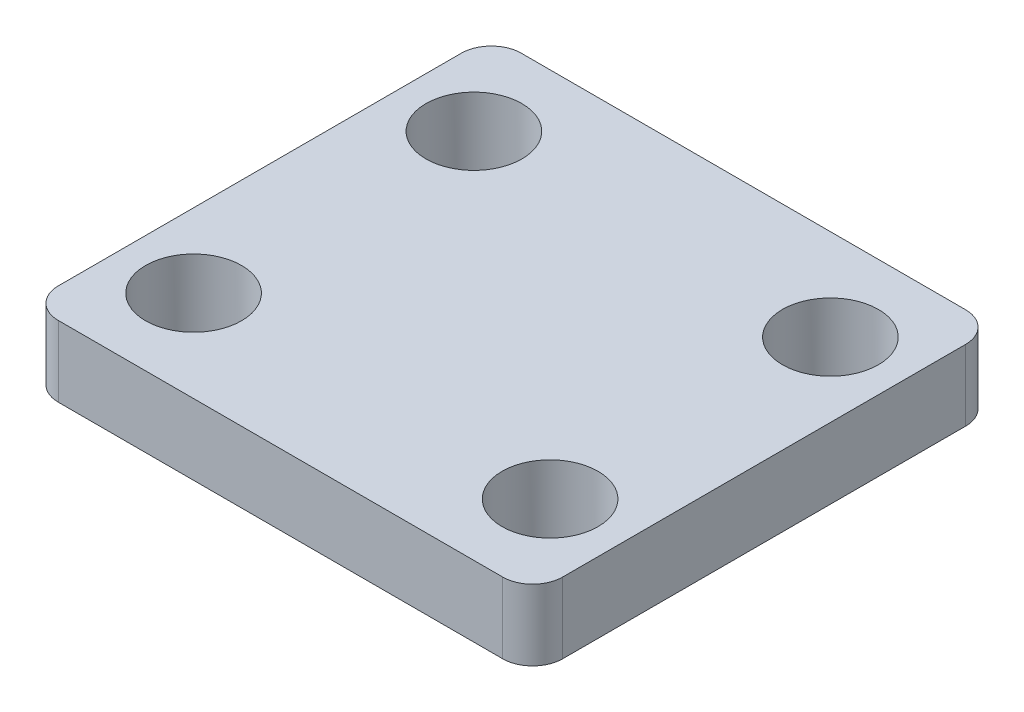
SolidWorks part; units mm, degrees
ref_plane "Plan de face" through (0, 0, 0) normal (0, 0, 1) x (1, 0, 0)
ref_plane "Plan de dessus" through (0, 0, 0) normal (0, 1, 0) x (1, 0, 0)
ref_plane "Plan de droite" through (0, 0, 0) normal (1, 0, 0) x (0, 0, -1)
ref_plane "Plan1" through (0, 12.573, 0) normal (0, 1, 0) x (1, 0, 0)
sketch "Esquisse1" plane through (0, 12.573, 0) normal (0, 1, 0) x (1, 0, 0)
  line L0 (-21.3614, 19.6088) -> (-21.3614, -19.6088)
  line L1 (-21.3614, -19.6088) -> (21.3614, -19.6088)
  line L2 (21.3614, -19.6088) -> (21.3614, 19.6088)
  line L3 (21.3614, 19.6088) -> (-21.3614, 19.6088)
extrude "Boss.-Extru.1" add sketch "Esquisse1" against normal blind 12.573
sketch "Esquisse2" plane through (0, 0, -19.6088) normal (0, 0, -1) x (-1, 0, 0)
  line L0 (-9.525, 12.573) -> (-6.985, 7.493)
  line L1 (-6.985, 7.493) -> (6.985, 7.493)
  line L2 (6.985, 7.493) -> (9.525, 12.573)
  line L3 (9.525, 12.573) -> (-9.525, 12.573)
extrude "Enlèv. mat.-Extru.1" cut sketch "Esquisse2" against normal through all
hole_wizard "Perçage1" positions "Esquisse4" profile "Esquisse3" legacy
sketch "Esquisse4" plane through (0, 12.573, 0) normal (0, 1, 0) x (1, 0, 0)
  point P0 (15.1003, -11.8745)
  point P1 (-15.1003, 11.8745)
  point P2 (15.1003, 11.8745)
  point P3 (-15.1003, -11.8745)
sketch "Esquisse3" plane through (15.1003, 12.573, 11.8745) normal (1, 0, 0) x (0, 0, 1)
  line L0 (0, 0) -> (0, 12.573)
  line L1 (0, 12.573) -> (4.064, 12.573)
  line L2 (4.064, 12.573) -> (4.064, 0)
  line L3 (4.064, 0) -> (0, 0)
  line L4 (0, 110) -> (0, -10) construction
  dimension "Diamètre" = 8.128
  dimension "Profondeur" = 12.573
fillet "Congé1" radius 0.254 4 edges at (-6.985, 7.493, 0) (9.525, 12.573, 0) (6.985, 7.493, 0) (-9.525, 12.573, 0)
fillet "Congé2" radius 2.54 4 edges at (-21.3614, 6.2865, -19.6088) (21.3614, 6.2865, -19.6088) (-21.3614, 6.2865, 19.6088) (21.3614, 6.2865, 19.6088)
sketch "Esquisse5" plane through (21.3614, 0, 0) normal (1, 0, 0) x (0, 0, -1)
  line L0 (-15.9385, 0) -> (-7.8105, 0) construction
  line L1 (-28.3554, 27.3402) -> (30.6518, 27.3402)
  line L2 (-28.3554, 27.3402) -> (-28.3554, 6)
  line L3 (-28.3554, 6) -> (30.6518, 6)
  line L4 (30.6518, 27.3402) -> (30.6518, 6)
  dimension "D1" = 6
extrude "Enlèv. mat.-Extru.2" cut sketch "Esquisse5" against normal through all
